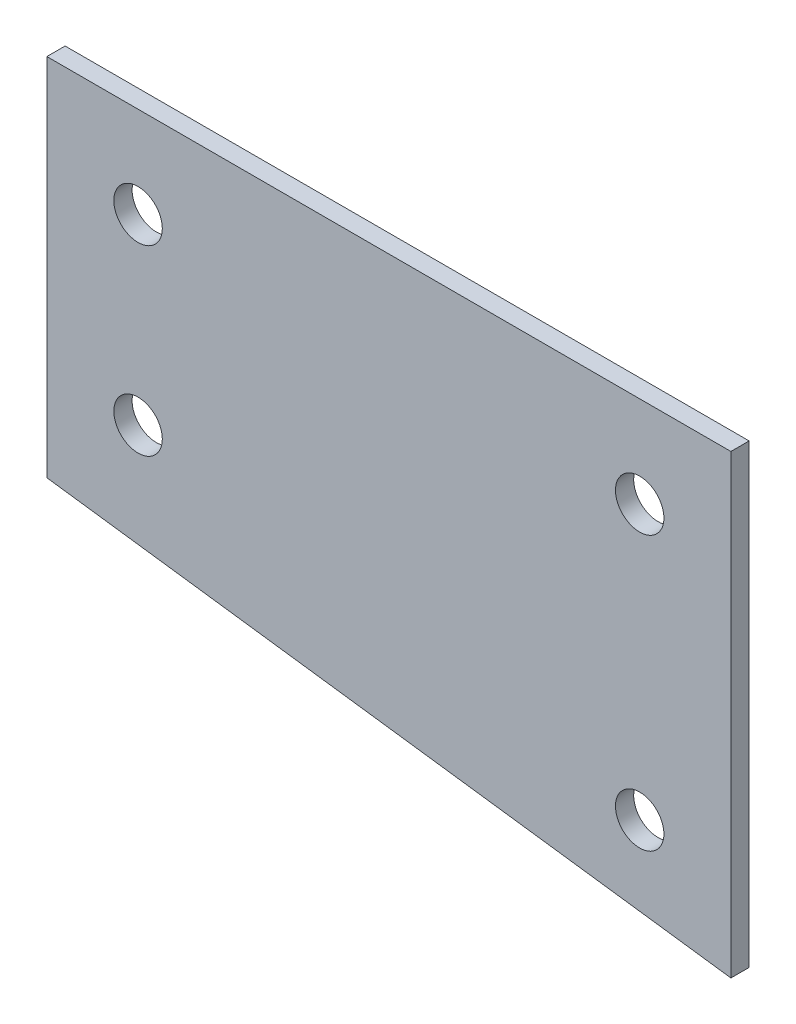
SolidWorks part; units mm, degrees
material "6061-T6 (SS)"
ref_plane "Front Plane" through (0, 0, 0) normal (0, 0, 1) x (1, 0, 0)
ref_plane "Top Plane" through (0, 0, 0) normal (0, 1, 0) x (1, 0, 0)
ref_plane "Right Plane" through (0, 0, 0) normal (1, 0, 0) x (0, 0, -1)
sketch "Sketch2" plane through (0, 0, 0) normal (0, 0, 1) x (1, 0, 0)
  line L0 (-95.25, -25.4) -> (-95.25, 25.4)
  line L1 (0, -38.1) -> (0, 38.1)
  line L2 (0, 38.1) -> (-95.25, 25.4)
  line L3 (0, 0) -> (-95.25, 0) construction
  line L4 (0, -38.1) -> (-95.25, -25.4)
  line L5 (-95.25, 25.4) -> (-95.25, 38.1)
  line L6 (-95.25, 38.1) -> (0, 38.1)
  line L7 (-95.25, -25.4) -> (-95.25, -38.1)
  line L8 (-95.25, -38.1) -> (0, -38.1)
  point P5 (-95.25, 0)
  dimension "D1" = 50.8
  dimension "D2" = 95.25
  dimension "D3" = 38.1
sketch "Sketch3" plane through (0, 0, 0) normal (0, 1, 0) x (1, 0, 0)
  line L0 (-127, 228.6) -> (-127, -228.6)
  line L1 (-95.25, 0) -> (0, 0) construction
  line L2 (-127, -228.6) -> (0, -228.6)
  line L3 (-127, 0) -> (-123.825, 0) construction
  line L4 (-123.825, 225.425) -> (-123.825, -225.425)
  line L6 (-123.825, -225.425) -> (0, -225.425)
  line L7 (0, -225.425) -> (0, -228.6)
  line L8 (0, 225.425) -> (0, 228.6)
  line L9 (-123.825, 225.425) -> (0, 225.425)
  line L10 (-127, 228.6) -> (0, 228.6)
  dimension "D1" = 127
  dimension "D2" = 3.175
  dimension "D3" = 3.175
  dimension "D4" = 225.425
extrude "Boss-Extrude3" add sketch "Sketch2" along normal mid plane 2.54 contours L3 L1 L2 L0 | L1 L3 L0 L4
sketch "Sketch4" plane through (0, 0, 1.27) normal (0, 0, 1) x (1, 0, 0)
  line L0 (0, 38.1) -> (0, 25.4)
  line L1 (0, -38.1) -> (0, 38.1) construction
  line L2 (0, 25.4) -> (-107.902, 25.4)
  line L3 (-107.902, 25.4) -> (-107.902, 38.1)
  line L4 (-107.902, 38.1) -> (0, 38.1)
  dimension "D1" = 12.7
extrude "Cut-Extrude1" cut sketch "Sketch4" against normal through all both and the other way through all
sketch "Sketch5" plane through (0, 0, 1.27) normal (0, 0, 1) x (1, 0, 0)
  line L0 (0, 0) -> (-41.0232, 0) construction
  line L1 (-95.25, 0) -> (-120.4138, 0) construction
  line L2 (0, -38.1) -> (0, 25.4) construction
  line L3 (-95.25, -25.4) -> (-95.25, 25.4) construction
  line L4 (-95.25, 25.4) -> (0, 25.4) construction
  circle A0 centre (-82.55, 12.7) radius 2.5797
  circle A1 centre (-82.55, -12.7) radius 2.5797
  circle A2 centre (-12.7, 12.7) radius 2.5797
  circle A3 centre (-12.7, -25.4) radius 2.5797
  point P15 (-89.6055, -11.6822)
  point P16 (-120.4138, 0)
  dimension "D1" = 5.1594
  dimension "D2" = 5.1594
  dimension "D3" = 5.1594
  dimension "D4" = 5.1594
  dimension "D5" = 25.4
  dimension "D6" = 38.1
  dimension "D7" = 12.7
  dimension "D8" = 12.7
  dimension "D9" = 12.7
  dimension "D10" = 12.7
hole_wizard "17/64 (0.26563) Diameter Hole1" positions "Sketch6" profile "Sketch7" hole size "17/64" standard "ANSI Inch" end condition through all
sketch "Sketch6" plane through (0, 0, 1.27) normal (0, 0, 1) x (1, 0, 0)
  point P0 (-82.55, 12.7)
  point P3 (-82.55, -12.7)
  point P6 (-12.7, -25.4)
  point P9 (-12.7, 12.7)
sketch "Sketch7" plane through (-82.55, 12.7, 1.27) normal (1, 0, 0) x (0, -1, 0)
  line L0 (0, 0) -> (0, 2.54)
  line L1 (0, 2.54) -> (3.3735, 2.54)
  line L2 (3.3735, 2.54) -> (3.3735, 0)
  line L5 (3.3735, 0) -> (0, 0)
  line L11 (0, -6.35) -> (0, 107.95) construction
  dimension "Thru Hole Dia." = 6.747
  dimension "Thru Hole Depth" = 2.54
